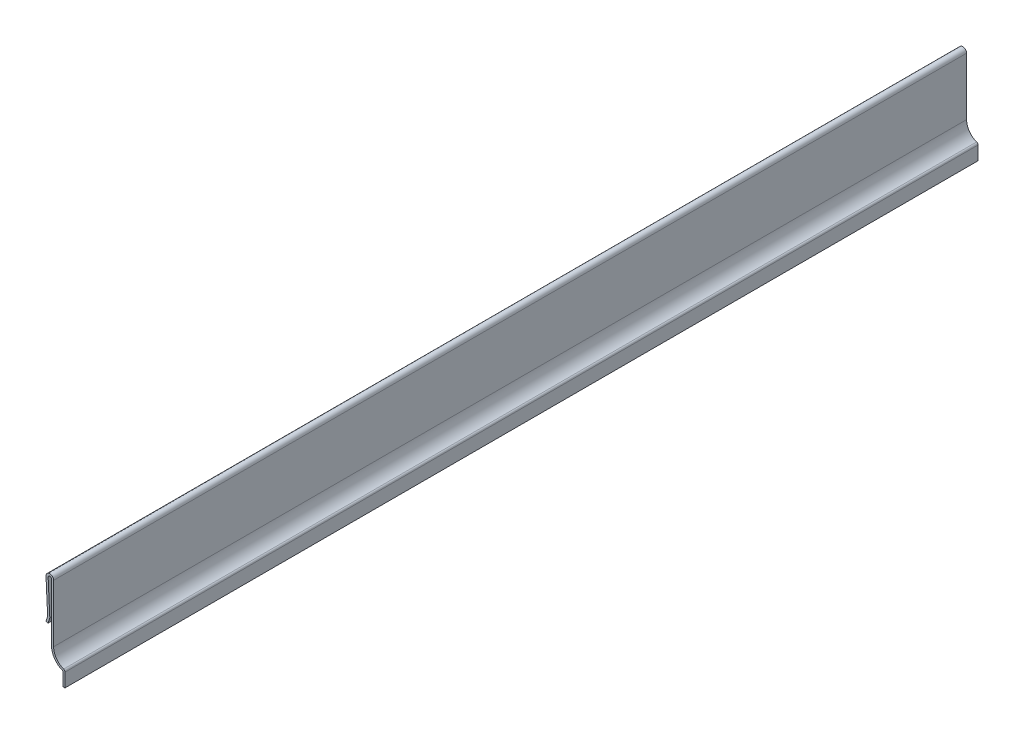
SolidWorks part; units mm, degrees
ref_plane "Front Plane" through (0, 0, 0) normal (0, 0, 1) x (1, 0, 0)
ref_plane "Top Plane" through (0, 0, 0) normal (0, 1, 0) x (1, 0, 0)
ref_plane "Right Plane" through (0, 0, 0) normal (1, 0, 0) x (0, 0, -1)
sketch "Sketch1" plane through (0, 0, 0) normal (0, 0, 1) x (1, 0, 0)
  line L0 (0, 0) -> (0, 6.35)
  line L1 (-4.7625, 12.4984) -> (-4.7625, 36.5125)
  line L2 (-7.9356, 36.4355) -> (-7.2459, 22.225)
  line L3 (-7.2459, 22.225) -> (-7.9375, 20.1214)
  line L4 (-0.889, 0) -> (-0.889, 5.6962)
  line L5 (-5.6515, 12.4984) -> (-5.6515, 36.5125)
  line L6 (-7.0477, 36.4786) -> (-6.358, 22.2681)
  line L7 (-6.4014, 21.9474) -> (-7.093, 19.8438)
  line L8 (0, 0) -> (-0.889, 0)
  line L9 (-7.9375, 20.1214) -> (-7.093, 19.8438)
  line L10 (-7.0477, 36.4786) -> (-6.35, 22.1037) construction
  line L11 (-6.35, 22.1037) -> (-7.093, 19.8438) construction
  arc A0 (0, 6.35) -> (-4.7625, 12.4984) centre (1.5875, 12.4984) cw
  arc A1 (-4.7625, 36.5125) -> (-7.9356, 36.4355) centre (-6.35, 36.5125) ccw
  arc A2 (-0.889, 5.6962) -> (-5.6515, 12.4984) centre (1.5875, 12.4984) cw
  arc A3 (-5.6515, 36.5125) -> (-7.0477, 36.4786) centre (-6.35, 36.5125) ccw
  arc A4 (-6.358, 22.2681) -> (-6.4014, 21.9474) centre (-7.2459, 22.225) cw
  point P24 (-6.35, 22.1037)
extrude "Boss-Extrude1" add sketch "Sketch1" against normal blind 381
fillet "Fillet1" radius 0.889 1 edges at (0, 6.35, -190.5)
equation "\"D1@Extrude-Thin1\"=\"D10@Sketch1\"*10"
